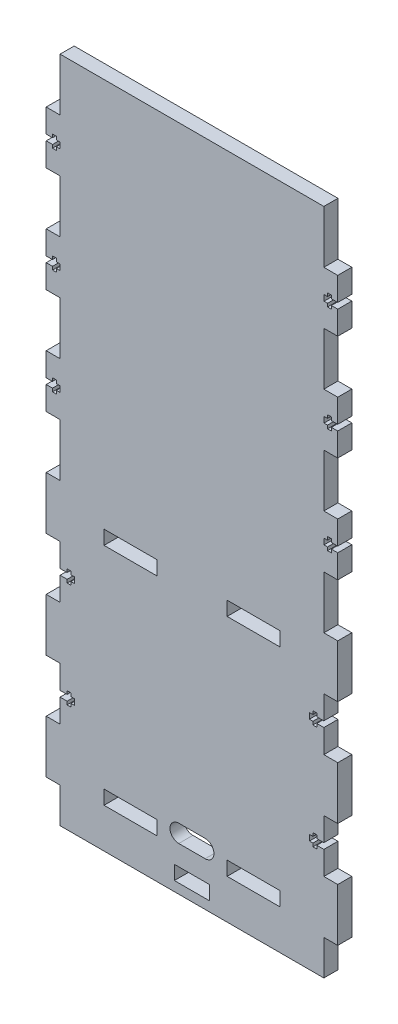
SolidWorks part; units mm, degrees
material "Acrylic (Medium-high impact)"
ref_plane "Front Plane" through (0, 0, 0) normal (0, 0, 1) x (1, 0, 0)
ref_plane "Top Plane" through (0, 0, 0) normal (0, 1, 0) x (1, 0, 0)
ref_plane "Right Plane" through (0, 0, 0) normal (1, 0, 0) x (0, 0, -1)
sketch "Sketch1" plane through (0, 0, 0) normal (0, 0, 1) x (1, 0, 0)
  line L1 (0, 0) -> (150, 0)
  line L2 (0, 0) -> (0, 380)
  line L3 (0, 380) -> (150, 380)
  line L4 (150, 0) -> (150, 380)
  line L5 (25, 158.5669) -> (55, 158.5669)
  line L6 (25, 158.5669) -> (25, 150.5669)
  line L7 (25, 150.5669) -> (55, 150.5669)
  line L8 (55, 158.5669) -> (55, 150.5669)
  line L9 (95, 158.5669) -> (125, 158.5669)
  line L10 (95, 158.5669) -> (95, 150.5669)
  line L11 (95, 150.5669) -> (125, 150.5669)
  line L12 (125, 158.5669) -> (125, 150.5669)
  line L13 (25, 30.5669) -> (55, 30.5669)
  line L14 (25, 30.5669) -> (25, 22.5669)
  line L15 (25, 22.5669) -> (55, 22.5669)
  line L16 (55, 30.5669) -> (55, 22.5669)
  line L17 (95, 30.5669) -> (125, 30.5669)
  line L18 (95, 30.5669) -> (95, 22.5669)
  line L19 (95, 22.5669) -> (125, 22.5669)
  line L20 (125, 30.5669) -> (125, 22.5669)
  line L21 (85, 5.5) -> (65, 5.5)
  line L22 (85, 5.5) -> (85, 13.5)
  line L23 (85, 13.5) -> (65, 13.5)
  line L24 (65, 5.5) -> (65, 13.5)
  dimension "D1" = 150
  dimension "D2" = 380
extrude "Boss-Extrude1" add sketch "Sketch1" along normal blind 8
sketch "Sketch2" plane through (0, 0, 8) normal (0, 0, 1) x (1, 0, 0)
  line L0 (150, 0) -> (150, 380) construction
  line L1 (150, 350) -> (157.9, 350)
  line L2 (150, 350) -> (150, 320)
  line L3 (150, 320) -> (157.9, 320)
  line L4 (157.9, 350) -> (157.9, 320)
  line L5 (150, 380) -> (0, 380) construction
  line L6 (-7.9, 350) -> (0, 350)
  line L7 (-7.9, 350) -> (-7.9, 320)
  line L8 (-7.9, 320) -> (0, 320)
  line L9 (0, 350) -> (0, 320)
  line L10 (150, 290) -> (157.9, 290)
  line L11 (150, 290) -> (150, 260)
  line L12 (150, 260) -> (157.9, 260)
  line L13 (157.9, 290) -> (157.9, 260)
  line L14 (-7.9, 290) -> (0, 290)
  line L15 (-7.9, 290) -> (-7.9, 260)
  line L16 (-7.9, 260) -> (0, 260)
  line L17 (0, 290) -> (0, 260)
  line L18 (150, 230) -> (157.9, 230)
  line L19 (150, 230) -> (150, 200)
  line L20 (150, 200) -> (157.9, 200)
  line L21 (157.9, 230) -> (157.9, 200)
  line L22 (75, 380) -> (75, 0) construction
  line L23 (0, 0) -> (150, 0) construction
  line L24 (-7.9, 230) -> (0, 230)
  line L25 (-7.9, 230) -> (-7.9, 200)
  line L26 (-7.9, 200) -> (0, 200)
  line L27 (0, 230) -> (0, 200)
  line L28 (150, 170) -> (157.9, 170)
  line L29 (150, 170) -> (150, 140)
  line L30 (150, 140) -> (157.9, 140)
  line L31 (157.9, 170) -> (157.9, 140)
  line L32 (-7.9, 170) -> (0, 170)
  line L33 (-7.9, 170) -> (-7.9, 140)
  line L34 (-7.9, 140) -> (0, 140)
  line L35 (0, 170) -> (0, 140)
  line L36 (150, 110) -> (157.9, 110)
  line L37 (150, 110) -> (150, 80)
  line L38 (150, 80) -> (157.9, 80)
  line L39 (157.9, 110) -> (157.9, 80)
  line L40 (-7.9, 110) -> (0, 110)
  line L41 (-7.9, 110) -> (-7.9, 80)
  line L42 (-7.9, 80) -> (0, 80)
  line L43 (0, 110) -> (0, 80)
  line L44 (150, 50) -> (157.9, 50)
  line L45 (150, 50) -> (150, 20)
  line L46 (150, 20) -> (157.9, 20)
  line L47 (157.9, 50) -> (157.9, 20)
  line L48 (-7.9, 50) -> (0, 50)
  line L49 (-7.9, 50) -> (-7.9, 20)
  line L50 (-7.9, 20) -> (0, 20)
  line L51 (0, 50) -> (0, 20)
  dimension "D1" = 7.9
  dimension "D2" = 30
  dimension "D3" = 30
  dimension "D4" = 2
extrude "Boss-Extrude2" add sketch "Sketch2" against normal blind 8
sketch "Sketch3" plane through (0, 0, 0) normal (0, 0, -1) x (-1, 0, 0)
  line L0 (-67.5, 30) -> (-82.5, 30) construction
  line L1 (-67.5, 25) -> (-82.5, 25)
  line L2 (-67.5, 35) -> (-82.5, 35)
  line L3 (7.9, 335) -> (-44.7856, 335) construction
  line L4 (0, 0) -> (-150, 0) construction
  line L5 (-75, 0) -> (-75, 380) construction
  line L6 (-150, 380) -> (0, 380) construction
  line L7 (0, 320) -> (0, 290) construction
  line L8 (7.9, 336.65) -> (4.3, 336.65)
  line L9 (4.3, 336.65) -> (4.3, 338.5)
  line L10 (4.3, 338.5) -> (2.1, 338.5)
  line L11 (2.1, 338.5) -> (2.1, 336.65)
  line L12 (2.1, 336.65) -> (0.1, 336.65)
  line L13 (0.1, 336.65) -> (0.1, 333.35)
  line L14 (7.9, 336.65) -> (7.9, 333.35)
  line L15 (2.1, 333.35) -> (0.1, 333.35)
  line L16 (2.1, 331.5) -> (2.1, 333.35)
  line L17 (4.3, 331.5) -> (2.1, 331.5)
  line L18 (4.3, 333.35) -> (4.3, 331.5)
  line L19 (7.9, 333.35) -> (4.3, 333.35)
  line L20 (0, 125) -> (-150, 125) construction
  line L21 (-157.9, 215) -> (-105.2144, 215) construction
  line L22 (-157.9, 275) -> (-105.2144, 275) construction
  line L23 (-157.9, 335) -> (-105.2144, 335) construction
  line L24 (-157.9, 213.35) -> (-154.3, 213.35)
  line L25 (-154.3, 213.35) -> (-154.3, 211.5)
  line L26 (-154.3, 211.5) -> (-152.1, 211.5)
  line L27 (-152.1, 211.5) -> (-152.1, 213.35)
  line L28 (-152.1, 213.35) -> (-150.1, 213.35)
  line L29 (-157.9, 216.65) -> (-157.9, 213.35)
  line L30 (-150.1, 216.65) -> (-150.1, 213.35)
  line L31 (-152.1, 216.65) -> (-150.1, 216.65)
  line L32 (-152.1, 218.5) -> (-152.1, 216.65)
  line L33 (-154.3, 218.5) -> (-152.1, 218.5)
  line L34 (-154.3, 216.65) -> (-154.3, 218.5)
  line L35 (-157.9, 216.65) -> (-154.3, 216.65)
  line L36 (-157.9, 273.35) -> (-154.3, 273.35)
  line L37 (-154.3, 273.35) -> (-154.3, 271.5)
  line L38 (-154.3, 271.5) -> (-152.1, 271.5)
  line L39 (-152.1, 271.5) -> (-152.1, 273.35)
  line L40 (-152.1, 273.35) -> (-150.1, 273.35)
  line L41 (-157.9, 276.65) -> (-157.9, 273.35)
  line L42 (-150.1, 276.65) -> (-150.1, 273.35)
  line L43 (-152.1, 276.65) -> (-150.1, 276.65)
  line L44 (-152.1, 278.5) -> (-152.1, 276.65)
  line L45 (-154.3, 278.5) -> (-152.1, 278.5)
  line L46 (-154.3, 276.65) -> (-154.3, 278.5)
  line L47 (7.9, 276.65) -> (4.3, 276.65)
  line L48 (4.3, 276.65) -> (4.3, 278.5)
  line L49 (4.3, 278.5) -> (2.1, 278.5)
  line L50 (2.1, 278.5) -> (2.1, 276.65)
  line L51 (2.1, 276.65) -> (0.1, 276.65)
  line L52 (0.1, 276.65) -> (0.1, 273.35)
  line L53 (7.9, 276.65) -> (7.9, 273.35)
  line L54 (2.1, 273.35) -> (0.1, 273.35)
  line L55 (2.1, 271.5) -> (2.1, 273.35)
  line L56 (4.3, 271.5) -> (2.1, 271.5)
  line L57 (4.3, 273.35) -> (4.3, 271.5)
  line L58 (7.9, 273.35) -> (4.3, 273.35)
  line L59 (7.9, 275) -> (-44.7856, 275) construction
  line L60 (7.9, 216.65) -> (4.3, 216.65)
  line L61 (4.3, 216.65) -> (4.3, 218.5)
  line L62 (4.3, 218.5) -> (2.1, 218.5)
  line L63 (2.1, 218.5) -> (2.1, 216.65)
  line L64 (2.1, 216.65) -> (0.1, 216.65)
  line L65 (0.1, 216.65) -> (0.1, 213.35)
  line L66 (7.9, 216.65) -> (7.9, 213.35)
  line L67 (2.1, 213.35) -> (0.1, 213.35)
  line L68 (2.1, 211.5) -> (2.1, 213.35)
  line L69 (4.3, 211.5) -> (2.1, 211.5)
  line L70 (4.3, 213.35) -> (4.3, 211.5)
  line L71 (7.9, 213.35) -> (4.3, 213.35)
  line L72 (7.9, 215) -> (-44.7856, 215) construction
  line L73 (-157.9, 276.65) -> (-154.3, 276.65)
  line L74 (-157.9, 333.35) -> (-154.3, 333.35)
  line L75 (-154.3, 333.35) -> (-154.3, 331.5)
  line L76 (-154.3, 331.5) -> (-152.1, 331.5)
  line L77 (-152.1, 331.5) -> (-152.1, 333.35)
  line L78 (-152.1, 333.35) -> (-150.1, 333.35)
  line L79 (-157.9, 336.65) -> (-157.9, 333.35)
  line L80 (-150.1, 336.65) -> (-150.1, 333.35)
  line L81 (-152.1, 336.65) -> (-150.1, 336.65)
  line L82 (-152.1, 338.5) -> (-152.1, 336.65)
  line L83 (-154.3, 338.5) -> (-152.1, 338.5)
  line L84 (-154.3, 336.65) -> (-154.3, 338.5)
  line L85 (7.9, 350) -> (7.9, 320) construction
  line L86 (0, 140) -> (0, 110) construction
  line L87 (-157.9, 336.65) -> (-154.3, 336.65)
  line L88 (-150, 110) -> (-150, 140) construction
  line L89 (0, 123.35) -> (0, 126.65)
  line L90 (0, 126.65) -> (-4, 126.65)
  line L91 (-4, 126.65) -> (-4, 128.5)
  line L92 (-4, 128.5) -> (-6.2, 128.5)
  line L93 (-6.2, 128.5) -> (-6.2, 126.65)
  line L94 (-6.2, 126.65) -> (-8.2, 126.65)
  line L95 (-8.2, 126.65) -> (-8.2, 123.35)
  line L96 (-6.2, 123.35) -> (-8.2, 123.35)
  line L97 (-6.2, 121.5) -> (-6.2, 123.35)
  line L98 (-4, 121.5) -> (-6.2, 121.5)
  line L99 (-4, 123.35) -> (-4, 121.5)
  line L100 (0, 123.35) -> (-4, 123.35)
  line L101 (0, 63.35) -> (0, 66.65)
  line L102 (0, 66.65) -> (-4, 66.65)
  line L103 (-4, 66.65) -> (-4, 68.5)
  line L104 (-4, 68.5) -> (-6.2, 68.5)
  line L105 (-6.2, 68.5) -> (-6.2, 66.65)
  line L106 (-6.2, 66.65) -> (-8.2, 66.65)
  line L107 (-8.2, 66.65) -> (-8.2, 63.35)
  line L108 (-6.2, 63.35) -> (-8.2, 63.35)
  line L109 (-6.2, 61.5) -> (-6.2, 63.35)
  line L110 (-4, 61.5) -> (-6.2, 61.5)
  line L111 (-4, 63.35) -> (-4, 61.5)
  line L112 (0, 63.35) -> (-4, 63.35)
  line L113 (0, 65) -> (-150, 65) construction
  line L114 (-150, 63.35) -> (-146, 63.35)
  line L115 (-146, 63.35) -> (-146, 61.5)
  line L116 (-146, 61.5) -> (-143.8, 61.5)
  line L117 (-143.8, 61.5) -> (-143.8, 63.35)
  line L118 (-143.8, 63.35) -> (-141.8, 63.35)
  line L119 (-141.8, 66.65) -> (-141.8, 63.35)
  line L120 (-143.8, 66.65) -> (-141.8, 66.65)
  line L121 (-143.8, 68.5) -> (-143.8, 66.65)
  line L122 (-146, 68.5) -> (-143.8, 68.5)
  line L123 (-146, 66.65) -> (-146, 68.5)
  line L124 (-150, 66.65) -> (-146, 66.65)
  line L125 (-150, 63.35) -> (-150, 66.65)
  line L126 (-150, 123.35) -> (-146, 123.35)
  line L127 (-146, 123.35) -> (-146, 121.5)
  line L128 (-146, 121.5) -> (-143.8, 121.5)
  line L129 (-143.8, 121.5) -> (-143.8, 123.35)
  line L130 (-143.8, 123.35) -> (-141.8, 123.35)
  line L131 (-141.8, 126.65) -> (-141.8, 123.35)
  line L132 (-143.8, 126.65) -> (-141.8, 126.65)
  line L133 (-143.8, 128.5) -> (-143.8, 126.65)
  line L134 (-146, 128.5) -> (-143.8, 128.5)
  line L135 (-146, 126.65) -> (-146, 128.5)
  line L136 (-150, 126.65) -> (-146, 126.65)
  line L137 (-150, 123.35) -> (-150, 126.65)
  arc A0 (-67.5, 25) -> (-67.5, 35) centre (-67.5, 30) ccw
  arc A1 (-82.5, 35) -> (-82.5, 25) centre (-82.5, 30) ccw
  point P2 (-75, 30)
  point P26 (7.9, 335)
  point P113 (-8.2, 125)
  point P130 (-8.2, 65)
  point P157 (-141.8, 65)
  point P161 (-141.8, 125)
  dimension "D2" = 5
  dimension "D1" = 15
  dimension "D3" = 3.3
  dimension "D4" = 25
  dimension "D5" = 7
  dimension "D6" = 2.2
  dimension "D7" = 0.1
  dimension "D8" = 2
  dimension "D9" = 4
  dimension "D10" = 2.2
  dimension "D11" = 2
  dimension "D12" = 3.3
  dimension "D13" = 7
  dimension "D15" = 3
extrude "Cut-Extrude2" cut sketch "Sketch3" against normal through all
